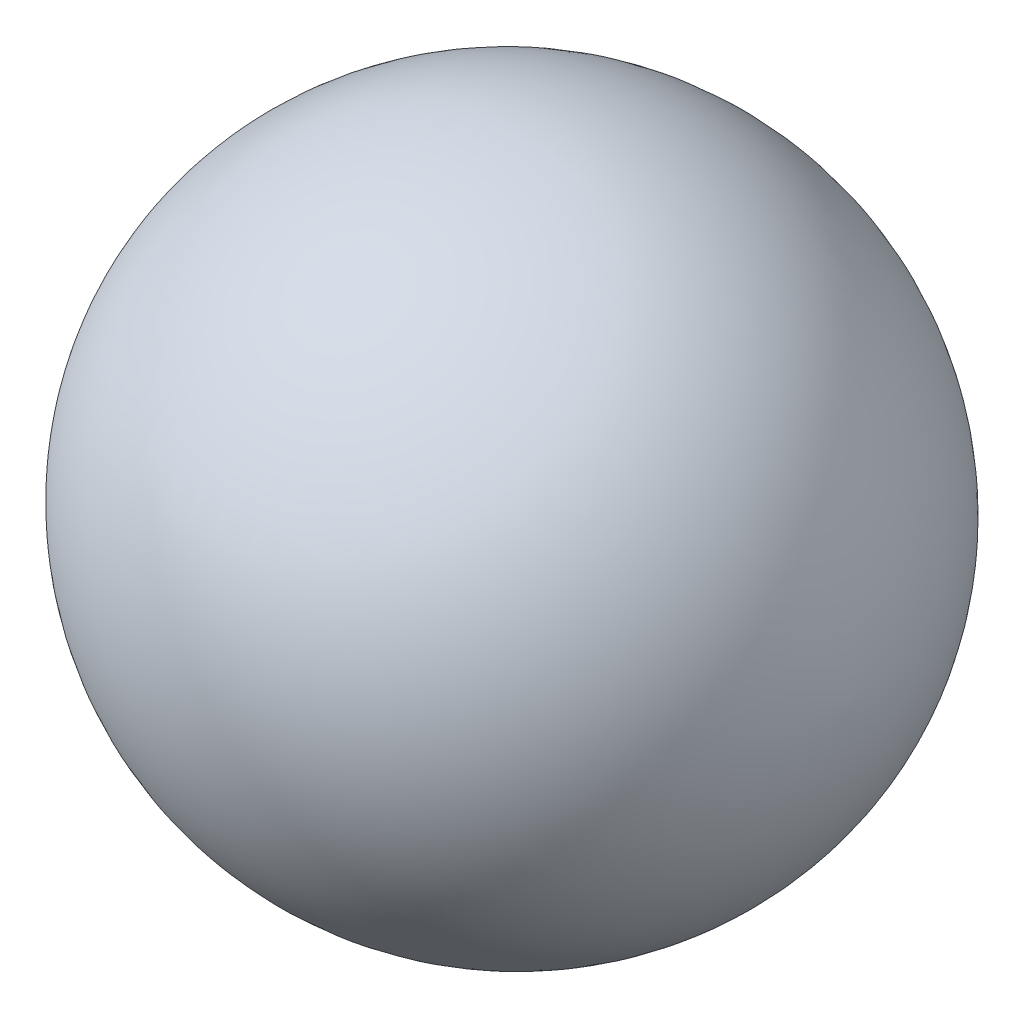
SolidWorks part; units mm, degrees
ref_plane "Front Plane" through (0, 0, 0) normal (0, 0, 1) x (1, 0, 0)
ref_plane "Top Plane" through (0, 0, 0) normal (0, 1, 0) x (1, 0, 0)
ref_plane "Right Plane" through (0, 0, 0) normal (1, 0, 0) x (0, 0, -1)
sketch "Sketch1" plane through (0, 0, 0) normal (0, 1, 0) x (1, 0, 0)
  line L0 (-304.8, 0) -> (304.8, 0)
  arc A0 (304.8, 0) -> (-304.8, 0) centre (0, 11.1219) cw
  point P4 (0, 0)
  dimension "D1" = 609.6
revolve "Revolve1" add sketch "Sketch1" angle 360 about L0
